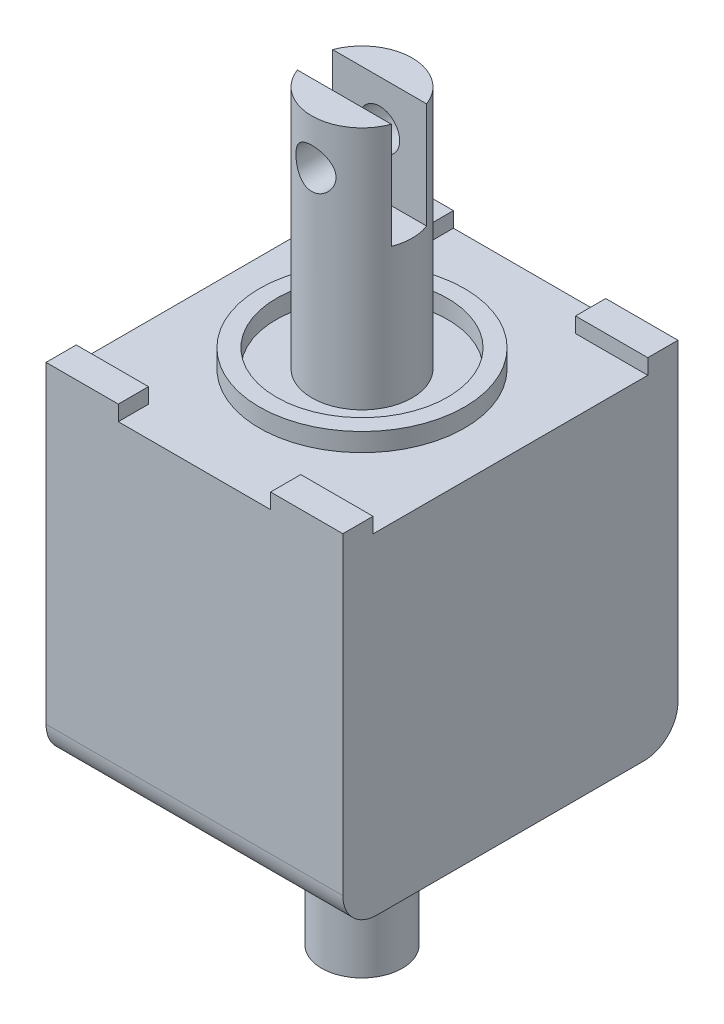
SolidWorks part; units mm, degrees
ref_plane "Front Plane" through (0, 0, 0) normal (0, 0, 1) x (1, 0, 0)
ref_plane "Top Plane" through (0, 0, 0) normal (0, 1, 0) x (1, 0, 0)
ref_plane "Right Plane" through (0, 0, 0) normal (1, 0, 0) x (0, 0, -1)
sketch "Sketch1" plane through (0, 0, 0) normal (0, 1, 0) x (1, 0, 0)
  line L1 (-11.1125, -12.5476) -> (11.1125, -12.5476)
  line L2 (-11.1125, -12.5476) -> (-11.1125, 12.5476)
  line L3 (-11.1125, 12.5476) -> (11.1125, 12.5476)
  line L4 (11.1125, -12.5476) -> (11.1125, 12.5476)
  line L5 (-11.1125, -12.5476) -> (11.1125, 12.5476) construction
  line L6 (-11.1125, 12.5476) -> (11.1125, -12.5476) construction
  point P0 (0, 0)
  dimension "D1" = 25.0952
  dimension "D2" = 22.225
extrude "Boss-Extrude1" add sketch "Sketch1" along normal blind 24.8666
sketch "Sketch2" plane through (0, 0, 0) normal (0, -1, 0) x (1, 0, 0)
  circle A0 centre (0, 0) radius 3.0226
  dimension "D1" = 6.0452
extrude "Boss-Extrude2" add sketch "Sketch2" along normal blind 12.4968
sketch "Sketch3" plane through (0, 24.8666, 0) normal (0, 1, 0) x (1, 0, 0)
  circle A0 centre (0, 0) radius 3.7592
  dimension "D1" = 7.5184
extrude "Boss-Extrude3" add sketch "Sketch3" along normal blind 18.288
sketch "Sketch4" plane through (0, 24.8666, 0) normal (0, 1, 0) x (1, 0, 0)
  circle A0 centre (0, 0) radius 7.6835
  circle A1 centre (0, 0) radius 6.4135
  dimension "D1" = 15.367
  dimension "D2" = 1.27
extrude "Boss-Extrude4" add sketch "Sketch4" along normal blind 1.3716
sketch "Sketch5" plane through (0, 24.8666, 0) normal (0, 1, 0) x (1, 0, 0)
  line L0 (-11.1125, -12.5476) -> (11.1125, -12.5476) construction
  line L1 (-11.1125, -12.5476) -> (-5.7023, -12.5476)
  line L2 (-11.1125, -12.5476) -> (-11.1125, -10.287)
  line L3 (-11.1125, -10.287) -> (-5.7023, -10.287)
  line L4 (-5.7023, -12.5476) -> (-5.7023, -10.287)
  line L5 (11.1125, -12.5476) -> (5.7023, -12.5476)
  line L6 (11.1125, -12.5476) -> (11.1125, -10.287)
  line L7 (11.1125, -10.287) -> (5.7023, -10.287)
  line L8 (5.7023, -12.5476) -> (5.7023, -10.287)
  line L9 (11.1125, -12.5476) -> (11.1125, 12.5476) construction
  line L10 (11.1125, 12.5476) -> (5.7023, 12.5476)
  line L11 (11.1125, 12.5476) -> (11.1125, 10.287)
  line L12 (11.1125, 10.287) -> (5.7023, 10.287)
  line L13 (5.7023, 12.5476) -> (5.7023, 10.287)
  line L14 (-11.1125, 12.5476) -> (-5.7023, 12.5476)
  line L15 (-11.1125, 12.5476) -> (-11.1125, 10.287)
  line L16 (-11.1125, 10.287) -> (-5.7023, 10.287)
  line L17 (-5.7023, 12.5476) -> (-5.7023, 10.287)
  dimension "D1" = 5.4102
  dimension "D2" = 2.2606
extrude "Boss-Extrude5" add sketch "Sketch5" along normal blind 1.143
fillet "Fillet1" radius 2.54 2 edges at (0, 0, -12.5476) (0, 0, 12.5476)
sketch "Sketch6" plane through (0, 0, 0) normal (1, 0, 0) x (0, 0, -1)
  line L0 (3.7592, 43.1546) -> (-3.7592, 43.1546) construction
  line L1 (-1.3208, 43.1546) -> (1.3208, 43.1546)
  line L2 (-1.3208, 43.1546) -> (-1.3208, 35.2298)
  line L3 (-1.3208, 35.2298) -> (1.3208, 35.2298)
  line L4 (1.3208, 43.1546) -> (1.3208, 35.2298)
  point P6 (0, 35.2298)
  dimension "D1" = 7.9248
  dimension "D2" = 2.6416
extrude "Cut-Extrude1" cut sketch "Sketch6" against normal up to surface and the other way up to surface up to face at (0, 43.1546, 3.7592) other way up to face at (0, 43.1546, 3.7592)
sketch "Sketch7" plane through (0, 0, 0) normal (0, 0, 1) x (1, 0, 0)
  line L1 (3.5195, 43.1546) -> (-3.5195, 43.1546) construction
  circle A0 centre (0, 39.751) radius 1.4986
  dimension "D1" = 1.905
  dimension "D2" = 2.9972
extrude "Cut-Extrude2" cut sketch "Sketch7" against normal up to surface and the other way up to surface up to face at (0, 39.1922, 0) other way up to face at (0, 39.1922, 0)
